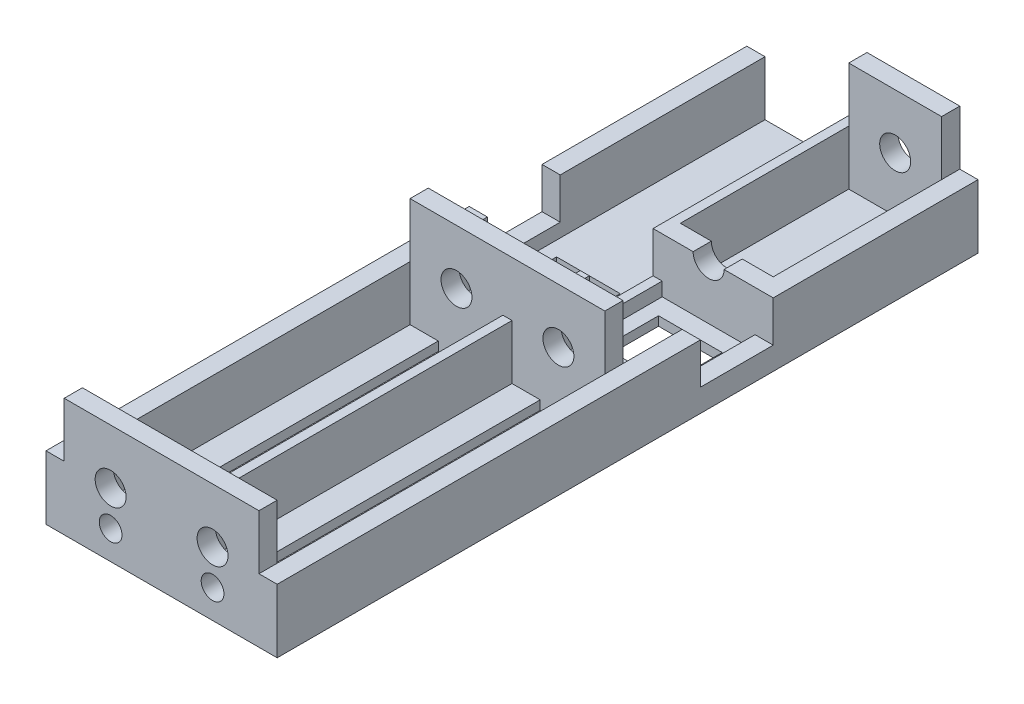
SolidWorks part; units mm, degrees
ref_plane "Front Plane" through (0, 0, 0) normal (0, 0, 1) x (1, 0, 0)
ref_plane "Top Plane" through (0, 0, 0) normal (0, 1, 0) x (1, 0, 0)
ref_plane "Right Plane" through (0, 0, 0) normal (1, 0, 0) x (0, 0, -1)
sketch "Sketch2" plane through (0, 0, 0) normal (0, 0, 1) x (1, 0, 0)
  line L0 (-24.5065, 76.6361) -> (-24.5065, 70.6361)
  line L1 (-24.5065, 76.6361) -> (-25.5065, 76.6361)
  line L2 (-25.5065, 76.6361) -> (-25.5065, 70.6361)
  line L3 (-13.3065, 70.6361) -> (-13.3065, 69.6361)
  line L4 (-36.7065, 70.6361) -> (-36.7065, 69.6361)
  line L5 (-36.7065, 69.6361) -> (-13.3065, 69.6361)
  line L6 (-24.5065, 70.6361) -> (-14.3065, 70.6361)
  line L7 (-35.7065, 70.6361) -> (-25.5065, 70.6361)
  line L8 (-14.3065, 70.6361) -> (-14.3065, 76.6361)
  line L9 (-14.3065, 76.6361) -> (-13.3065, 76.6361)
  line L10 (-36.7065, 76.6361) -> (-37.7065, 76.6361)
  line L11 (-13.3065, 76.6361) -> (-13.3065, 70.6361)
  line L12 (-37.7065, 76.6361) -> (-37.7065, 69.6361)
  line L13 (-37.7065, 69.6361) -> (-36.7065, 69.6361)
  line L14 (-13.3065, 76.6361) -> (-12.3065, 76.6361)
  line L15 (-12.3065, 76.6361) -> (-12.3065, 69.6361)
  line L16 (-12.3065, 69.6361) -> (-13.3065, 69.6361)
  line L18 (-36.7065, 70.6361) -> (-36.7065, 76.6361)
  line L19 (-36.7065, 76.6361) -> (-35.7065, 76.6361)
  line L20 (-35.7065, 76.6361) -> (-35.7065, 70.6361)
extrude "Gearbox Mount" add sketch "Sketch2" along normal blind 77
sketch "Sketch7" plane through (0, 0, 0) normal (0, 0, 1) x (1, 0, 0)
  line L0 (-24.5065, 70.6361) -> (-24.5065, 82.6361)
  line L1 (-19.4065, 76.6361) -> (-8.2065, 76.6361) construction
  line L2 (-25.5065, 82.6361) -> (-24.5065, 82.6361)
  line L3 (-35.7065, 70.6361) -> (-35.7065, 82.6361)
  line L4 (-35.7065, 82.6361) -> (-25.5065, 82.6361)
  line L5 (-19.4065, 70.6361) -> (-19.4065, 76.6361) construction
  line L7 (-19.4065, 76.6361) -> (-30.6065, 76.6361) construction
  line L8 (-24.5065, 82.6361) -> (-14.3065, 82.6361)
  line L9 (-14.3065, 82.6361) -> (-14.3065, 70.6361)
  line L10 (-14.3065, 70.6361) -> (-24.5065, 70.6361)
  line L11 (-25.5065, 82.6361) -> (-25.5065, 70.6361)
  line L12 (-25.5065, 70.6361) -> (-35.7065, 70.6361)
  line L17 (-25.5065, 76.6361) -> (-24.5065, 76.6361)
  line L19 (-13.3065, 76.6361) -> (-14.3065, 76.6361)
  circle A0 centre (-19.4065, 76.6361) radius 1.7
  circle A1 centre (-30.6065, 76.6361) radius 1.7
extrude "Boss-Extrude6" add sketch "Sketch7" against normal mid plane 2 from offset 38
sketch "Sketch8" plane through (0, 0, 0) normal (0, 0, 1) x (1, 0, 0)
  line L0 (-30.6065, 76.6361) -> (-19.4065, 76.6361) construction
  line L1 (-19.4065, 76.6361) -> (-8.2065, 76.6361) construction
  line L2 (-35.7065, 70.6361) -> (-35.7065, 82.6361)
  line L3 (-35.7065, 82.6361) -> (-25.5065, 82.6361)
  line L4 (-25.5065, 82.6361) -> (-24.5065, 82.6361)
  line L5 (-24.5065, 76.6361) -> (-25.5065, 76.6361)
  line L6 (-25.5065, 82.6361) -> (-25.5065, 70.6361)
  line L7 (-24.5065, 82.6361) -> (-14.3065, 82.6361)
  line L8 (-25.5065, 70.6361) -> (-35.7065, 70.6361)
  line L9 (-24.5065, 70.6361) -> (-24.5065, 82.6361)
  line L11 (-14.3065, 82.6361) -> (-14.3065, 70.6361)
  line L13 (-14.3065, 70.6361) -> (-24.5065, 70.6361)
  line L17 (-13.3065, 76.6361) -> (-14.3065, 76.6361)
  line L25 (-30.6065, 74.9361) -> (-30.6065, 70.6361) construction
  line L26 (-19.4065, 74.9361) -> (-19.4065, 70.6361) construction
  line L27 (-30.6065, 78.3361) -> (-30.6065, 82.6361) construction
  line L28 (-19.4065, 78.3361) -> (-19.4065, 82.6361) construction
  circle A0 centre (-19.4065, 76.6361) radius 1.7
  circle A1 centre (-30.6065, 76.6361) radius 1.7
  circle A2 centre (-30.6065, 72.7861) radius 1.25
  circle A3 centre (-19.4065, 72.7861) radius 1.25
extrude "Boss-Extrude7" add sketch "Sketch8" against normal mid plane 2 from offset 76
sketch "Sketch9" plane through (0, 0, 0) normal (0, 0, 1) x (1, 0, 0)
  line L0 (-27.1065, 70.6361) -> (-27.1065, 69.6361)
  line L2 (-27.1065, 69.6361) -> (-34.1065, 69.6361)
  line L3 (-34.1065, 69.6361) -> (-34.1065, 70.6361)
  line L4 (-30.6065, 70.6361) -> (-30.6065, 69.6361) construction
  line L5 (-15.9065, 70.6361) -> (-15.9065, 69.6361)
  line L6 (-27.1065, 70.6361) -> (-34.1065, 70.6361)
  line L7 (-15.9065, 69.6361) -> (-22.9065, 69.6361)
  line L8 (-22.9065, 69.6361) -> (-22.9065, 70.6361)
  line L9 (-22.9065, 70.6361) -> (-15.9065, 70.6361)
  line L10 (-19.4065, 70.6361) -> (-19.4065, 69.6361) construction
sketch "Sketch10" plane through (0, 0, 0) normal (0, 0, 1) x (1, 0, 0)
  line L0 (-14.3065, 82.6361) -> (-12.3065, 82.6361) construction
  line L1 (-14.3065, 70.6361) -> (-14.3065, 72.1361)
  line L3 (-12.3065, 82.6361) -> (-37.7065, 82.6361)
  line L4 (-12.3065, 82.6361) -> (-12.3065, 72.1361)
  line L5 (-14.3065, 70.6361) -> (-24.5065, 70.6361)
  line L6 (-37.7065, 72.1361) -> (-37.7065, 82.6361)
  line L7 (-14.3065, 76.6361) -> (-14.3065, 70.6361) construction
  line L8 (-14.3065, 72.1361) -> (-12.3065, 72.1361)
  line L9 (-35.7065, 70.6361) -> (-35.7065, 72.1361)
  line L10 (-35.7065, 70.6361) -> (-35.7065, 76.6361) construction
  line L11 (-35.7065, 72.1361) -> (-37.7065, 72.1361)
  line L12 (-24.5065, 70.6361) -> (-24.5065, 72.1361)
  line L13 (-24.5065, 76.6361) -> (-24.5065, 70.6361) construction
  line L14 (-24.5065, 72.1361) -> (-25.5065, 72.1361)
  line L15 (-25.5065, 76.6361) -> (-25.5065, 70.6361) construction
  line L16 (-25.5065, 72.1361) -> (-25.5065, 70.6361)
  line L17 (-35.7065, 70.6361) -> (-25.5065, 70.6361) construction
  line L18 (-25.5065, 70.6361) -> (-35.7065, 70.6361)
extrude "Cut-Extrude1" cut sketch "Sketch10" along normal blind 8 from offset 22.5
sketch "Sketch11" plane through (0, 0, 0) normal (0, 0, 1) x (1, 0, 0)
  line L0 (-24.5065, 70.6361) -> (-24.5065, 82.6361)
  line L1 (-19.4065, 76.6361) -> (-8.2065, 76.6361) construction
  line L2 (-14.3065, 76.6361) -> (-24.5065, 76.6361)
  line L5 (-19.4065, 70.6361) -> (-19.4065, 76.6361) construction
  line L7 (-19.4065, 76.6361) -> (-30.6065, 76.6361) construction
  line L8 (-24.5065, 82.6361) -> (-14.3065, 82.6361)
  line L9 (-14.3065, 82.6361) -> (-14.3065, 70.6361)
  line L10 (-14.3065, 70.6361) -> (-24.5065, 70.6361)
  line L19 (-13.3065, 76.6361) -> (-14.3065, 76.6361)
  circle A0 centre (-19.4065, 76.6361) radius 1.7
extrude "Boss-Extrude9" add sketch "Sketch11" against normal blind 2 from offset 22.5
sketch "Sketch12" plane through (0, 0, 0) normal (0, 0, 1) x (1, 0, 0)
  line L0 (-24.5065, 70.6361) -> (-24.5065, 82.6361)
  line L1 (-19.4065, 76.6361) -> (-8.2065, 76.6361) construction
  line L5 (-19.4065, 70.6361) -> (-19.4065, 76.6361) construction
  line L7 (-19.4065, 76.6361) -> (-30.6065, 76.6361) construction
  line L8 (-24.5065, 82.6361) -> (-14.3065, 82.6361)
  line L9 (-14.3065, 82.6361) -> (-14.3065, 70.6361)
  line L10 (-14.3065, 70.6361) -> (-24.5065, 70.6361)
  line L19 (-13.3065, 76.6361) -> (-14.3065, 76.6361)
  circle A0 centre (-19.4065, 76.6361) radius 1.7
extrude "Boss-Extrude10" add sketch "Sketch12" along normal blind 2 contours L10 L9 L8 L0 A0
extrude "Cut-Extrude2" cut sketch "Sketch9" along normal blind 6 from offset 24.5
sketch "Sketch13" plane through (0, 0, 0) normal (0, 0, 1) x (1, 0, 0)
  line L0 (-19.4065, 69.6361) -> (-19.4065, 70.6361) construction
  line L1 (-37.7065, 69.6361) -> (-12.3065, 69.6361) construction
  line L2 (-19.4065, 69.6361) -> (-21.4065, 69.6361)
  line L3 (-30.6065, 69.6361) -> (-30.6065, 70.6361) construction
  line L4 (-21.4065, 69.6361) -> (-21.4065, 70.6361)
  line L5 (-21.4065, 70.6361) -> (-17.4065, 70.6361)
  line L6 (-17.4065, 70.6361) -> (-17.4065, 69.6361)
  line L7 (-17.4065, 69.6361) -> (-19.4065, 69.6361)
  line L8 (-30.6065, 69.6361) -> (-32.6065, 69.6361)
  line L9 (-32.6065, 69.6361) -> (-32.6065, 70.6361)
  line L10 (-35.7065, 70.6361) -> (-25.5065, 70.6361) construction
  line L11 (-32.6065, 70.6361) -> (-28.6065, 70.6361)
  line L12 (-25.5065, 70.6361) -> (-35.7065, 70.6361) construction
  line L13 (-28.6065, 70.6361) -> (-28.6065, 69.6361)
  line L14 (-28.6065, 69.6361) -> (-30.6065, 69.6361)
extrude "Cut-Extrude3" cut sketch "Sketch13" along normal blind 36 from offset 39
